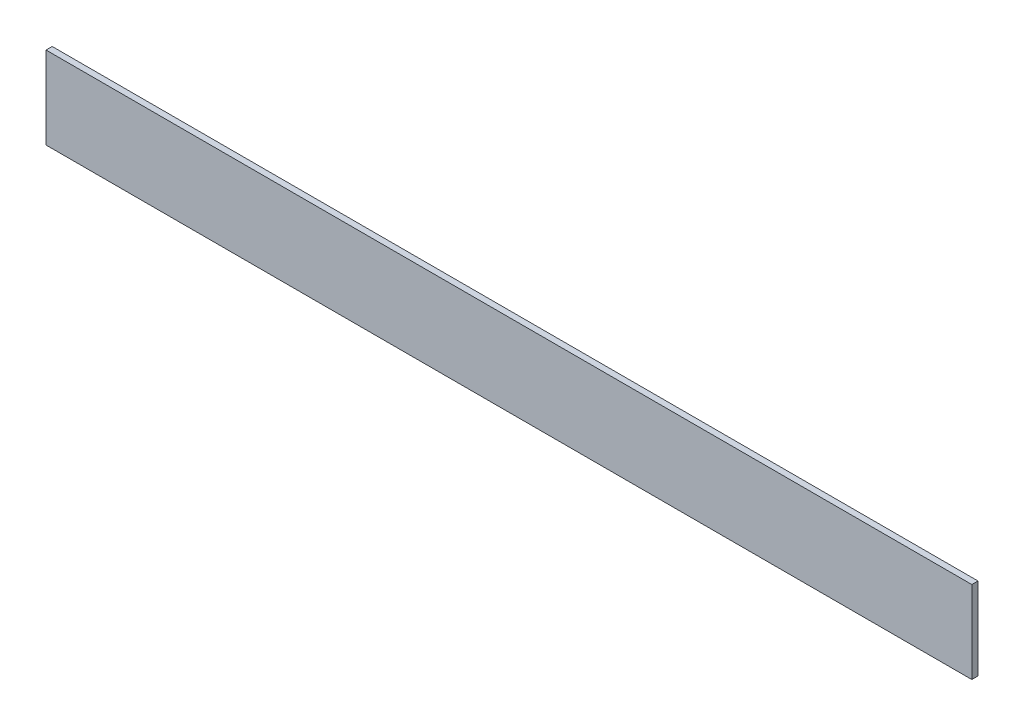
SolidWorks part; units mm, degrees
material "PA 类型 6"
ref_plane "前视基准面" through (0, 0, 0) normal (0, 0, 1) x (1, 0, 0)
ref_plane "上视基准面" through (0, 0, 0) normal (0, 1, 0) x (1, 0, 0)
ref_plane "右视基准面" through (0, 0, 0) normal (1, 0, 0) x (0, 0, -1)
other "Configuration Table"
sketch "草图1" plane through (0, 0, 0) normal (0, 0, 1) x (1, 0, 0)
  line L1 (-141.9155, 80.2255) -> (308.0845, 80.2255)
  line L2 (-141.9155, 80.2255) -> (-141.9155, 40.2255)
  line L3 (-141.9155, 40.2255) -> (308.0845, 40.2255)
  line L4 (308.0845, 80.2255) -> (308.0845, 40.2255)
  dimension "D1" = 450
  dimension "D2" = 40
extrude "凸台-拉伸1" add sketch "草图1" along normal blind 3
